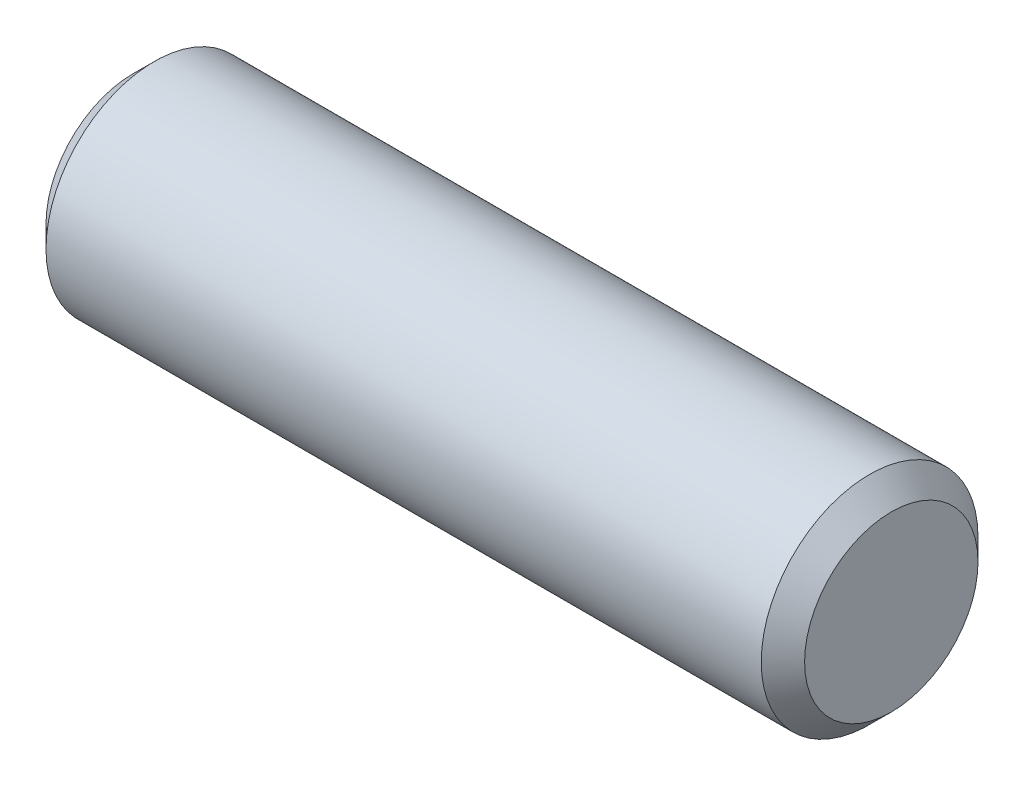
SolidWorks part; units mm, degrees
ref_plane "Front" through (0, 0, 0) normal (0, 0, 1) x (1, 0, 0)
ref_plane "Top" through (0, 0, 0) normal (0, 1, 0) x (1, 0, 0)
ref_plane "Right" through (0, 0, 0) normal (1, 0, 0) x (0, 0, -1)
sketch "Sketch1" plane through (0, 0, 0) normal (0, 0, 1) x (1, 0, 0)
  line L0 (-11.1125, 0) -> (11.1125, 0) construction
  line L1 (11.1125, 3.175) -> (11.1125, -3.175) construction
  line L2 (-11.1125, 3.175) -> (-11.1125, -3.175) construction
  dimension "Length" = 22.225
  dimension "Diameter" = 6.35
sketch "Sketch2" plane through (0, 0, 0) normal (1, 0, 0) x (0, 0, -1)
  circle A0 centre (0, 0) radius 3.175
extrude "Extrude1" add sketch "Sketch2" against normal up to vertex (11.1125 mm away) and the other way up to vertex (11.1125 mm away) up to point (-11.1125, 3.175, 0) other way up to point (11.1125, 3.175, 0)
chamfer "Chamfer1" distance 0.635 angle 45 2 edges at (11.1125, 0, -3.175) (-11.1125, 0, -3.175)
equation "\"D1@Chamfer1\" = \"Diameter@Sketch1\"*.1"
